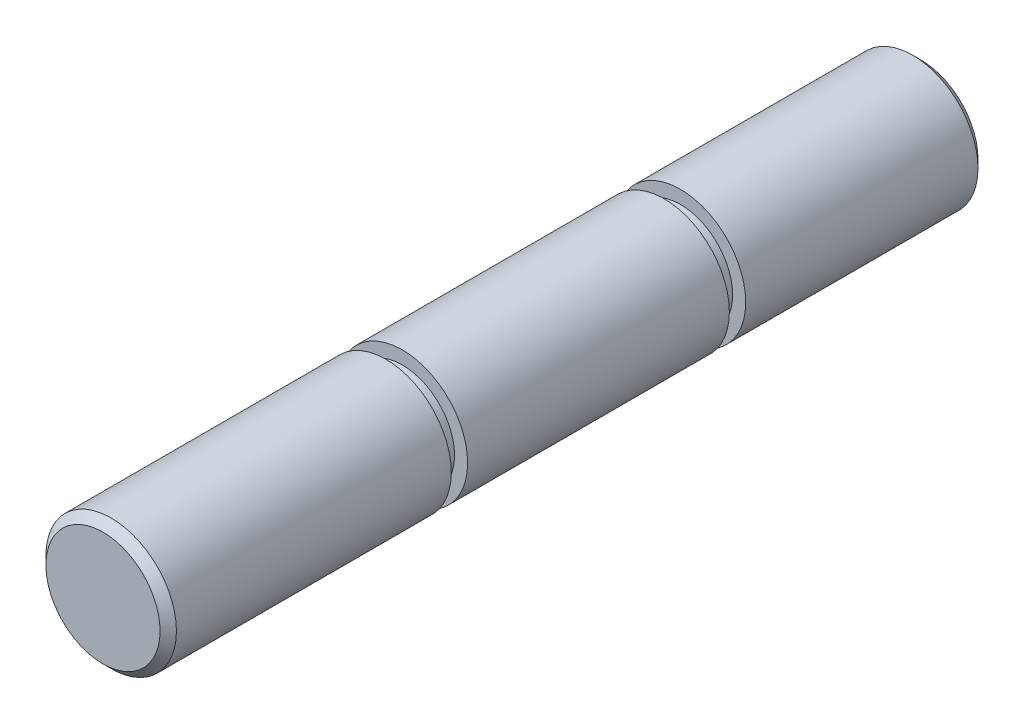
SolidWorks part; units mm, degrees
material "AISI 1015 Acero estirado en frío (SS)"
ref_plane "Alzado" through (0, 0, 0) normal (0, 0, 1) x (1, 0, 0)
ref_plane "Planta" through (0, 0, 0) normal (0, 1, 0) x (1, 0, 0)
ref_plane "Vista lateral" through (0, 0, 0) normal (1, 0, 0) x (0, 0, -1)
sketch "Croquis1" plane through (0, 0, 0) normal (0, 0, 1) x (1, 0, 0)
  circle A0 centre (0, 0) radius 3.99
  dimension "D1" = 7.98
extrude "Saliente-Extruir1" add sketch "Croquis1" along normal blind 50
sketch "Croquis2" plane through (0, 0, 0) normal (1, 0, 0) x (0, 0, -1)
  line L0 (0, 3.99) -> (-50, 3.99) construction
  line L1 (0, -3.99) -> (0, 3.99) construction
  line L3 (-14.7, 3.99) -> (-15.7, 3.99)
  line L4 (-14.7, 3.99) -> (-14.7, 3.19)
  line L5 (-14.7, 3.19) -> (-15.7, 3.19)
  line L6 (-15.7, 3.99) -> (-15.7, 3.19)
  line L7 (-31.7, 3.99) -> (-32.7, 3.99)
  line L8 (-31.7, 3.99) -> (-31.7, 3.19)
  line L9 (-31.7, 3.19) -> (-32.7, 3.19)
  line L10 (-32.7, 3.99) -> (-32.7, 3.19)
  dimension "D1" = 0.8
  dimension "D2" = 0.8
  dimension "D3" = 1
  dimension "D4" = 1
  dimension "D5" = 14.7
  dimension "D6" = 16
ref_axis "Eje1" through (0, 0, 50) along (0, 0, -1)
revolve "Cortar-Revolución1" cut sketch "Croquis2" angle 360 about axis through (0, 0, 50) along (0, 0, -1)
chamfer "Chaflán1" distance 0.5 angle 45 2 edges at (3.99, 0, 50) (3.99, 0, 0)
